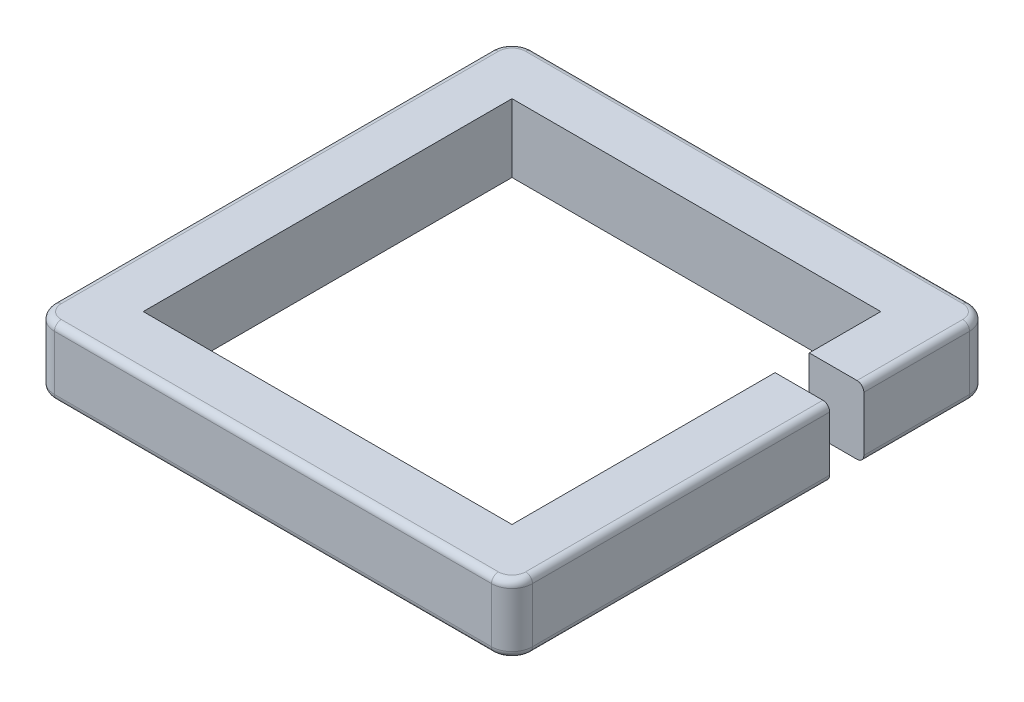
SolidWorks part; units mm, degrees
ref_plane "Front Plane" through (0, 0, 0) normal (0, 0, 1) x (1, 0, 0)
ref_plane "Top Plane" through (0, 0, 0) normal (0, 1, 0) x (1, 0, 0)
ref_plane "Right Plane" through (0, 0, 0) normal (1, 0, 0) x (0, 0, -1)
sketch "Sketch1" plane through (0, 0, 0) normal (0, 1, 0) x (1, 0, 0)
  line L0 (-444.5, 444.5) -> (-444.5, -444.5)
  line L1 (-342.9, 342.9) -> (342.9, 342.9)
  line L2 (-342.9, 342.9) -> (-342.9, -342.9)
  line L3 (-342.9, -342.9) -> (342.9, -342.9)
  line L4 (342.9, 342.9) -> (342.9, -342.9)
  line L5 (-342.9, 342.9) -> (342.9, -342.9) construction
  line L6 (-342.9, -342.9) -> (342.9, 342.9) construction
  line L7 (-444.5, -444.5) -> (444.5, -444.5)
  line L8 (444.5, 444.5) -> (444.5, -444.5)
  line L9 (-444.5, 444.5) -> (444.5, 444.5)
  point P0 (0, 0)
  dimension "D1" = 685.8
  dimension "D2" = 685.8
  dimension "D3" = 101.6
extrude "Boss-Extrude1" add sketch "Sketch1" along normal blind 127
fillet "Fillet1" radius 38.1 4 edges at (-444.5, 63.5, -444.5) (444.5, 63.5, -444.5) (444.5, 63.5, 444.5) (-444.5, 63.5, 444.5)
fillet "Fillet2" radius 12.7 16 edges at (433.3408, 0, 433.3408) (0, 0, 444.5) (-433.3408, 0, 433.3408) (-444.5, 0, 0) (-433.3408, 0, -433.3408) (0, 0, -444.5) (433.3408, 0, -433.3408) (433.3408, 127, 433.3408) (0, 127, 444.5) (-433.3408, 127, 433.3408) (-444.5, 127, 0) (-433.3408, 127, -433.3408) (0, 127, -444.5) (433.3408, 127, -433.3408) (444.5, 0, 0) (444.5, 127, 0)
sketch "Sketch2" plane through (0, 127, 0) normal (0, 1, 0) x (1, 0, 0)
  line L0 (342.9, -342.9) -> (342.9, 342.9) construction
  line L1 (342.9, 146.304) -> (444.5, 146.304)
  line L2 (342.9, 146.304) -> (342.9, 209.804)
  line L3 (342.9, 209.804) -> (444.5, 209.804)
  line L4 (444.5, 146.304) -> (444.5, 209.804)
  line L5 (444.5, 406.4) -> (444.5, -406.4) construction
  line L10 (324.2642, 209.804) -> (336.1358, 209.804) construction
  dimension "D1" = 63.5
extrude "Cut-Extrude1" cut sketch "Sketch2" against normal through all
